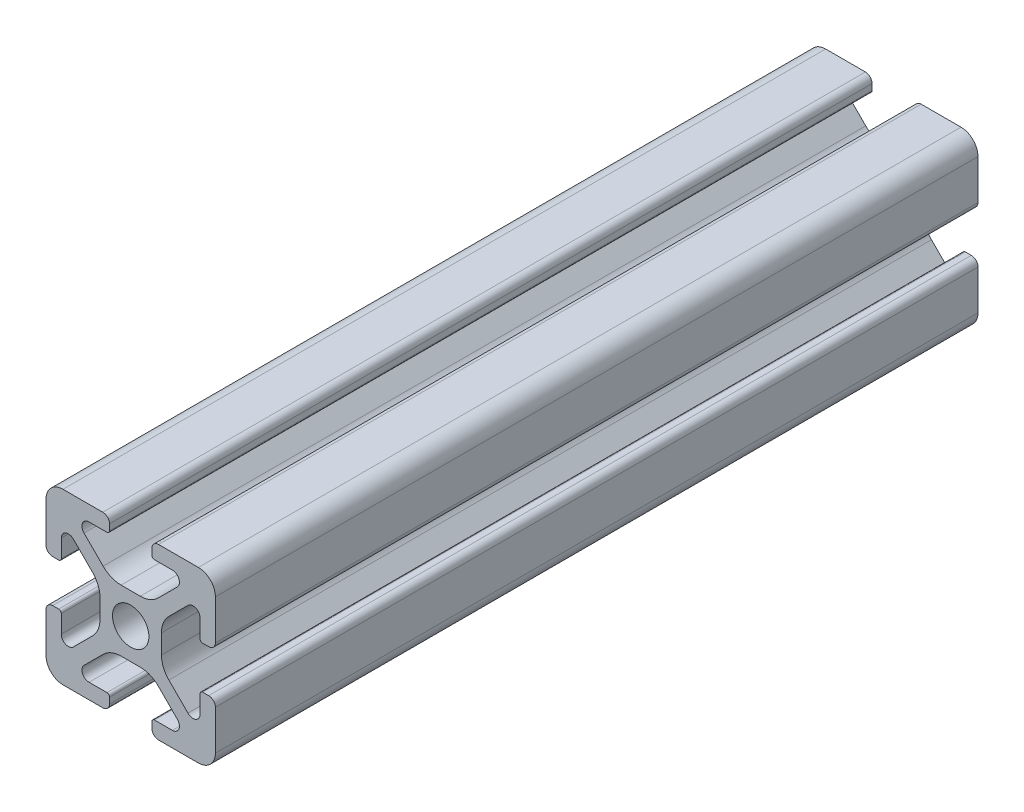
SolidWorks part; units mm, degrees
ref_plane "Front Plane" through (0, 0, 0) normal (0, 0, 1) x (1, 0, 0)
ref_plane "Top Plane" through (0, 0, 0) normal (0, 1, 0) x (1, 0, 0)
ref_plane "Right Plane" through (0, 0, 0) normal (1, 0, 0) x (0, 0, -1)
sketch "Sketch1" plane through (0, 0, 0) normal (0, 0, 1) x (1, 0, 0)
  line L2 (-9.9949, 7.9883) -> (-9.9949, 3.2893)
  line L3 (-7.9883, 9.9949) -> (-3.2893, 9.9949)
  line L4 (-2.5019, 9.2075) -> (-2.5019, 8.4963)
  line L5 (-2.8067, 8.1915) -> (-4.9149, 8.1915)
  line L6 (-5.5076, 6.7606) -> (-3.2528, 4.5058)
  line L7 (-6.7606, 5.5076) -> (-4.5058, 3.2528)
  line L8 (-8.1915, 4.9149) -> (-8.1915, 2.8067)
  line L9 (-8.4963, 2.5019) -> (-9.2075, 2.5019)
  line L11 (-1.1334, 3.6279) -> (1.1334, 3.6279)
  line L12 (-3.6279, 1.1334) -> (-3.6279, -1.1334)
  line L13 (8.4963, 2.5019) -> (9.2075, 2.5019)
  line L14 (8.1915, 4.9149) -> (8.1915, 2.8067)
  line L15 (9.9949, 7.9883) -> (9.9949, 3.2893)
  line L16 (7.9883, 9.9949) -> (3.2893, 9.9949)
  line L17 (2.5019, 9.2075) -> (2.5019, 8.4963)
  line L18 (2.8067, 8.1915) -> (4.9149, 8.1915)
  line L19 (3.6279, 1.1334) -> (3.6279, -1.1334)
  line L20 (5.5076, 6.7606) -> (3.2528, 4.5058)
  line L21 (6.7606, 5.5076) -> (4.5058, 3.2528)
  line L22 (-8.4963, -2.5019) -> (-9.2075, -2.5019)
  line L23 (-8.1915, -4.9149) -> (-8.1915, -2.8067)
  line L24 (-6.7606, -5.5076) -> (-4.5058, -3.2528)
  line L25 (-5.5076, -6.7606) -> (-3.2528, -4.5058)
  line L26 (-2.8067, -8.1915) -> (-4.9149, -8.1915)
  line L27 (-2.5019, -9.2075) -> (-2.5019, -8.4963)
  line L28 (-7.9883, -9.9949) -> (-3.2893, -9.9949)
  line L29 (-9.9949, -7.9883) -> (-9.9949, -3.2893)
  line L30 (9.9949, -7.9883) -> (9.9949, -3.2893)
  line L31 (7.9883, -9.9949) -> (3.2893, -9.9949)
  line L32 (2.5019, -9.2075) -> (2.5019, -8.4963)
  line L33 (2.8067, -8.1915) -> (4.9149, -8.1915)
  line L34 (5.5076, -6.7606) -> (3.2528, -4.5058)
  line L35 (6.7606, -5.5076) -> (4.5058, -3.2528)
  line L36 (8.1915, -4.9149) -> (8.1915, -2.8067)
  line L37 (8.4963, -2.5019) -> (9.2075, -2.5019)
  line L38 (-1.1334, -3.6279) -> (1.1334, -3.6279)
  circle A0 centre (0, 0) radius 2.1463
  arc A1 (-9.9949, 7.9883) -> (-7.9883, 9.9949) centre (-7.9883, 7.9883) cw
  arc A2 (-6.7606, 5.5076) -> (-8.1915, 4.9149) centre (-7.3533, 4.9149) ccw
  arc A3 (-4.9149, 8.1915) -> (-5.5076, 6.7606) centre (-4.9149, 7.3533) ccw
  arc A4 (-3.2893, 9.9949) -> (-2.5019, 9.2075) centre (-3.2893, 9.2075) cw
  arc A5 (-9.9949, 3.2893) -> (-9.2075, 2.5019) centre (-9.2075, 3.2893) ccw
  arc A6 (-8.1915, 2.8067) -> (-8.4963, 2.5019) centre (-8.4963, 2.8067) cw
  arc A7 (-2.5019, 8.4963) -> (-2.8067, 8.1915) centre (-2.8067, 8.4963) cw
  arc A8 (-1.1334, 3.6279) -> (-3.2528, 4.5058) centre (-1.1334, 6.6251) cw
  arc A9 (-3.6279, 1.1334) -> (-4.5058, 3.2528) centre (-6.6251, 1.1334) ccw
  arc A10 (8.1915, 2.8067) -> (8.4963, 2.5019) centre (8.4963, 2.8067) ccw
  arc A11 (9.9949, 3.2893) -> (9.2075, 2.5019) centre (9.2075, 3.2893) cw
  arc A12 (9.9949, 7.9883) -> (7.9883, 9.9949) centre (7.9883, 7.9883) ccw
  arc A13 (3.2893, 9.9949) -> (2.5019, 9.2075) centre (3.2893, 9.2075) ccw
  arc A14 (2.5019, 8.4963) -> (2.8067, 8.1915) centre (2.8067, 8.4963) ccw
  arc A15 (1.1334, 3.6279) -> (3.2528, 4.5058) centre (1.1334, 6.6251) ccw
  arc A16 (3.6279, 1.1334) -> (4.5058, 3.2528) centre (6.6251, 1.1334) cw
  arc A17 (6.7606, 5.5076) -> (8.1915, 4.9149) centre (7.3533, 4.9149) cw
  arc A18 (4.9149, 8.1915) -> (5.5076, 6.7606) centre (4.9149, 7.3533) cw
  arc A19 (-3.6279, -1.1334) -> (-4.5058, -3.2528) centre (-6.6251, -1.1334) cw
  arc A20 (-1.1334, -3.6279) -> (-3.2528, -4.5058) centre (-1.1334, -6.6251) ccw
  arc A21 (-2.5019, -8.4963) -> (-2.8067, -8.1915) centre (-2.8067, -8.4963) ccw
  arc A22 (-8.1915, -2.8067) -> (-8.4963, -2.5019) centre (-8.4963, -2.8067) ccw
  arc A23 (-9.9949, -3.2893) -> (-9.2075, -2.5019) centre (-9.2075, -3.2893) cw
  arc A24 (-3.2893, -9.9949) -> (-2.5019, -9.2075) centre (-3.2893, -9.2075) ccw
  arc A25 (-4.9149, -8.1915) -> (-5.5076, -6.7606) centre (-4.9149, -7.3533) cw
  arc A26 (-6.7606, -5.5076) -> (-8.1915, -4.9149) centre (-7.3533, -4.9149) cw
  arc A27 (-9.9949, -7.9883) -> (-7.9883, -9.9949) centre (-7.9883, -7.9883) ccw
  arc A28 (9.9949, -7.9883) -> (7.9883, -9.9949) centre (7.9883, -7.9883) cw
  arc A29 (6.7606, -5.5076) -> (8.1915, -4.9149) centre (7.3533, -4.9149) ccw
  arc A30 (4.9149, -8.1915) -> (5.5076, -6.7606) centre (4.9149, -7.3533) ccw
  arc A31 (3.2893, -9.9949) -> (2.5019, -9.2075) centre (3.2893, -9.2075) cw
  arc A32 (9.9949, -3.2893) -> (9.2075, -2.5019) centre (9.2075, -3.2893) ccw
  arc A33 (8.1915, -2.8067) -> (8.4963, -2.5019) centre (8.4963, -2.8067) cw
  arc A34 (2.5019, -8.4963) -> (2.8067, -8.1915) centre (2.8067, -8.4963) cw
  arc A35 (1.1334, -3.6279) -> (3.2528, -4.5058) centre (1.1334, -6.6251) cw
  arc A36 (3.6279, -1.1334) -> (4.5058, -3.2528) centre (6.6251, -1.1334) ccw
extrude "Boss-Extrude1" add sketch "Sketch1" along normal mid plane 90
